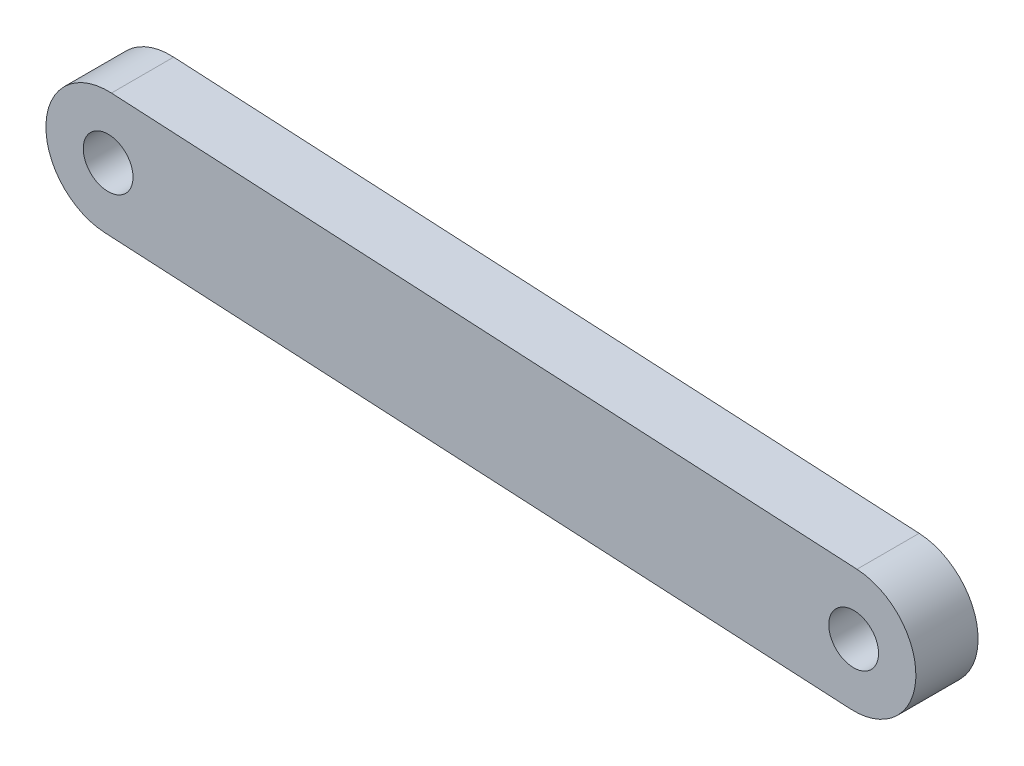
SolidWorks part; units mm, degrees
ref_plane "Front Plane" through (0, 0, 0) normal (0, 0, 1) x (1, 0, 0)
ref_plane "Top Plane" through (0, 0, 0) normal (0, 1, 0) x (1, 0, 0)
ref_plane "Right Plane" through (0, 0, 0) normal (1, 0, 0) x (0, 0, -1)
sketch "Sketch1" plane through (0, 0, 0) normal (0, 0, 1) x (0.4312, 0.9023, 0)
  line L0 (-23.2742, 28.2643) -> (-18.6548, 30.1777) construction
  line L1 (-18.6548, 30.1777) -> (-27.8936, 26.3509) construction
  line L2 (-18.6548, 30.1777) -> (-41.6158, 85.6105)
  line L3 (-27.8936, 26.3509) -> (-50.8546, 81.7837)
  line L4 (-41.6158, 85.6105) -> (-50.8546, 81.7837) construction
  circle A0 centre (-23.2742, 28.2643) radius 2
  arc A1 (-27.8936, 26.3509) -> (-18.6548, 30.1777) centre (-23.2742, 28.2643) ccw
  arc A2 (-50.8546, 81.7837) -> (-41.6158, 85.6105) centre (-46.2352, 83.6971) cw
  circle A3 centre (-46.2352, 83.6971) radius 2
  dimension "D1" = 10
  dimension "D3" = 5
  dimension "D4" = 4
  dimension "D5" = 4
  dimension "D6" = 5
  dimension "D2" = 60
extrude "Boss-Extrude1" add sketch "Sketch1" along normal blind 5
